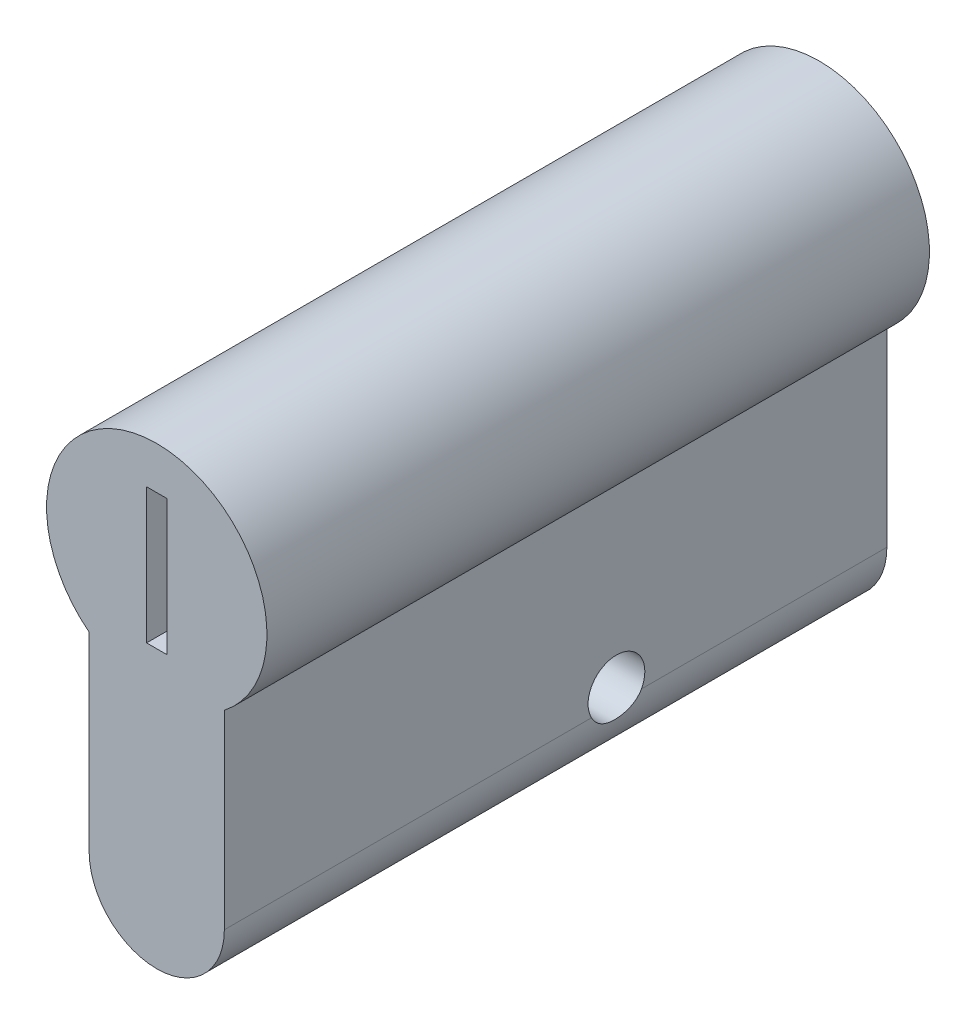
SolidWorks part; units mm, degrees
ref_plane "Plan de face" through (0, 0, 0) normal (0, 0, 1) x (1, 0, 0)
ref_plane "Plan de dessus" through (0, 0, 0) normal (0, 1, 0) x (1, 0, 0)
ref_plane "Plan de droite" through (0, 0, 0) normal (1, 0, 0) x (0, 0, -1)
sketch "Esquisse1" plane through (0, 0, 0) normal (0, 0, 1) x (1, 0, 0)
  line L0 (-5, -20.5) -> (-5, -6.8739) construction
  line L1 (-5, -20.5) -> (-5, -6.436)
  line L2 (5, -6.8739) -> (5, -20.5) construction
  line L3 (5, -6.436) -> (5, -20.5)
  line L5 (0.75, 5) -> (-0.75, 5)
  line L6 (0.75, 5) -> (0.75, -5)
  line L7 (0.75, -5) -> (-0.75, -5)
  line L8 (-0.75, 5) -> (-0.75, -5)
  arc A0 (5, -6.436) -> (-5, -6.436) centre (0, 0) ccw
  arc A2 (-5, -20.5) -> (5, -20.5) centre (0, -20.5) ccw construction
  arc A3 (-5, -20.5) -> (5, -20.5) centre (0, -20.5) ccw
  dimension "D1" = 16.3
  dimension "D2" = 1.5
  dimension "D3" = 0.75
  dimension "D4" = 10
  dimension "D5" = 5
sketch "Esquisse2" plane through (0, 0, 17.5) normal (0, 0, 1) x (1, 0, 0)
  line L2 (-5, -6.436) -> (-5, -20.5)
  line L3 (5, -20.5) -> (5, -6.436)
  line L4 (0.75, 5) -> (-0.75, 5)
  line L5 (-0.75, 5) -> (-0.75, -5)
  line L6 (-0.75, -5) -> (0.75, -5)
  line L7 (0.75, -5) -> (0.75, 5)
  line L8 (0.75, 5) -> (-0.75, 5)
  line L9 (-0.75, 5) -> (-0.75, -5)
  line L10 (-0.75, -5) -> (0.75, -5)
  line L11 (0.75, -5) -> (0.75, 5)
  line L12 (-5, -6.436) -> (-5, -20.5)
  line L13 (5, -20.5) -> (5, -6.436)
  arc A2 (5, -6.436) -> (-5, -6.436) centre (0, 0) ccw
  arc A3 (-5, -20.5) -> (5, -20.5) centre (0, -20.5) ccw
  arc A4 (5, -6.436) -> (-5, -6.436) centre (0, 0) ccw
  arc A5 (-5, -20.5) -> (5, -20.5) centre (0, -20.5) ccw
  dimension "D1" = 0
  dimension "D2" = 0
extrude "Extrusion2" add sketch "Esquisse2" along normal blind 9 and the other way blind 40
hole_wizard "Trou taraudé M51" positions "Esquisse3D1" profile "Esquisse4" tap size "M5" standard "ISO" end condition through all
sketch3d "Esquisse3D1"
  line L0 (34, -19.5, -2.5) -> (32, -19.5, -2.5) construction
  point P0 (-5, -19.5, -2.5)
sketch "Esquisse4" plane through (-5, -19.5, -2.5) normal (0, 1, 0) x (0, 0, 1)
  line L0 (0, 0) -> (0, 13.15)
  line L1 (0, 13.15) -> (2.1, 13.15)
  line L2 (2.1, 13.15) -> (2.1, 0)
  line L5 (2.1, 0) -> (0, 0)
  line L11 (0, -6.35) -> (0, 107.95) construction
  dimension "Diamètre du trou pour taraudage jusqu'au prochain" = 4.2
  dimension "Profondeur du trou pour taraudage jusqu'au prochain" = 13.15
cosmetic thread "Filetage de perçage1" parameters "D2"=5
